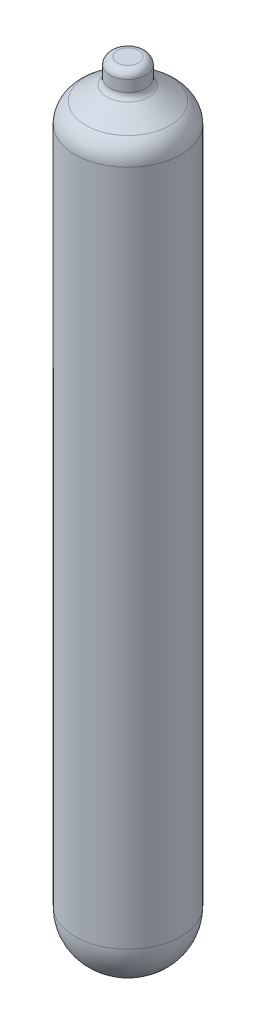
SolidWorks part; units mm, degrees
ref_plane "Спереди" through (0, 0, 0) normal (0, 0, 1) x (1, 0, 0)
ref_plane "Сверху" through (0, 0, 0) normal (0, 1, 0) x (1, 0, 0)
ref_plane "Справа" through (0, 0, 0) normal (1, 0, 0) x (0, 0, -1)
sketch "Эскиз1" plane through (0, 0, 0) normal (0, 0, 1) x (1, 0, 0)
  line L0 (0, 0) -> (10, 0)
  line L1 (110, 100) -> (110, 1507.6174)
  line L2 (87.7573, 1549.205) -> (43.9616, 1578.4361)
  line L3 (37.2888, 1590.9124) -> (37.2888, 1614.1588)
  line L4 (22.2888, 1629.1588) -> (0, 1629.1588)
  line L5 (0, 1629.1588) -> (0, 0)
  line L6 (0, 1553.0759) -> (0, -134.0499) construction
  arc A0 (43.9616, 1578.4361) -> (37.2888, 1590.9124) centre (52.2888, 1590.9124) cw
  arc A1 (37.2888, 1614.1588) -> (22.2888, 1629.1588) centre (22.2888, 1614.1588) ccw
  arc A2 (110, 1507.6174) -> (87.7573, 1549.205) centre (60, 1507.6174) ccw
  arc A3 (10, 0) -> (110, 100) centre (10, 100) ccw
  point P17 (110, 0)
  dimension "D1" = 15
  dimension "D2" = 50
  dimension "D3" = 100
revolve "Повернуть1" add sketch "Эскиз1" angle 360 about L6
